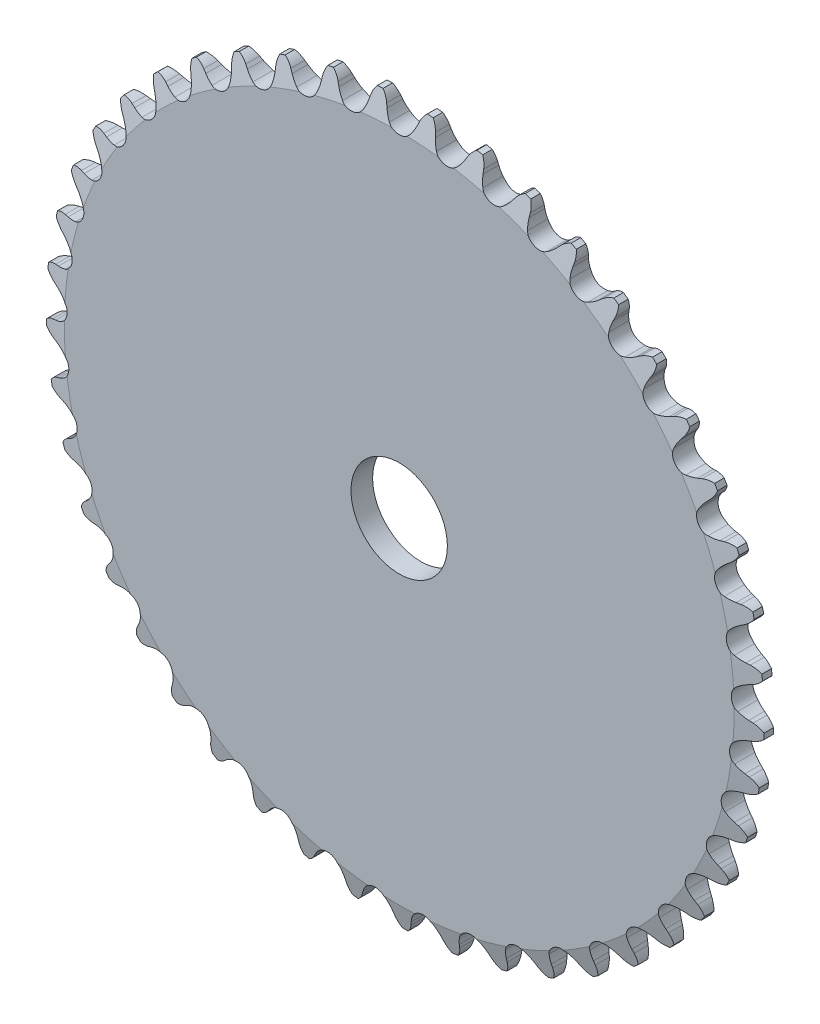
SolidWorks part; units mm, degrees
ref_plane "Front Plane" through (0, 0, 0) normal (0, 0, 1) x (1, 0, 0)
ref_plane "Top Plane" through (0, 0, 0) normal (0, 1, 0) x (1, 0, 0)
ref_plane "Right Plane" through (0, 0, 0) normal (1, 0, 0) x (0, 0, -1)
sketch "Sketch0" plane through (0, 0, 0) normal (0, 0, 1) x (1, 0, 0)
  line L0 (4.7625, -68.1069) -> (0, 0) construction
  line L1 (0, 0) -> (14.1948, -66.7813) construction
  line L2 (0, 0) -> (-4.7625, -68.1069) construction
  line L3 (4.7625, -68.1069) -> (14.1948, -66.7813) construction
  line L4 (4.7625, -68.1069) -> (-4.7625, -68.1069) construction
  line L5 (8.0591, -68.7521) -> (7.7638, -68.0754)
  line L6 (4.7625, -68.1069) -> (0, -68.4399) construction
  line L7 (1.5878, -69.2046) -> (1.786, -68.4934)
  line L8 (0, -68.1069) -> (0, -70.9644) construction
  line L9 (6.7374, -66.4301) -> (1.6645, -70.7373) construction
  line L10 (0, 0) -> (0, -68.1069) construction
  line L11 (7.7638, -68.0754) -> (1.6645, -70.7373) construction
  line L12 (0, -70.9644) -> (0, -71.4516) construction
  line L13 (11.8053, -67.1171) -> (8.0591, -68.7521) construction
  circle A0 centre (0, 0) radius 70.9644 construction
  circle A1 centre (0, 0) radius 68.2732 construction
  arc A2 (-2.4904, -72.1919) -> (12.5134, -71.1427) centre (0, 0) ccw
  circle A3 centre (0, 0) radius 71.4516 construction
  circle A4 centre (4.7625, -68.1069) radius 2.54 construction
  arc A7 (6.7374, -66.4301) -> (2.5734, -66.7212) centre (4.7625, -68.1069) ccw
  circle A8 centre (4.7625, -68.1069) radius 2.5908 construction
  arc A9 (8.0591, -68.7521) -> (12.5134, -71.1427) centre (11.8053, -67.1171) ccw
  arc A10 (7.7638, -68.0754) -> (6.7374, -66.4301) centre (1.6645, -70.7373) ccw
  arc A11 (1.5878, -69.2046) -> (-2.4904, -72.1919) centre (-2.3495, -68.1069) cw
  arc A12 (1.786, -68.4934) -> (2.5734, -66.7212) centre (8.1964, -70.2805) cw
  dimension "D1" = 2.5908
  dimension "R" = 2.5908
sketch "Sketch1" plane through (0, 0, 0) normal (1, 0, 0) x (0, 0, -1)
  line L0 (2.1336, 0) -> (-2.1336, 0)
  line L1 (-2.1336, 0) -> (-2.1336, 66.2019)
  line L2 (-2.1336, 66.2019) -> (-0.943, 70.9644)
  line L3 (-0.943, 70.9644) -> (0.943, 70.9644)
  line L4 (0.943, 70.9644) -> (2.1336, 66.2019)
  line L5 (2.1336, 66.2019) -> (2.1336, 0)
  line L7 (0, 70.9644) -> (0, 0) construction
  line L8 (-2.1336, 66.2019) -> (2.1336, 66.2019) construction
  line L9 (0, 70.9644) -> (0, -70.9644) construction
  line L10 (-2.1336, 66.2019) -> (-2.1336, 70.9644) construction
  line L11 (-2.1336, 70.9644) -> (-0.943, 70.9644) construction
  line L12 (0.943, 70.9644) -> (2.1336, 70.9644) construction
  line L13 (2.1336, 70.9644) -> (2.1336, 66.2019) construction
revolve "Revolve1" add sketch "Sketch1" angle 360 mid plane about L0
extrude "Cut-Extrude1" cut sketch "Sketch0" against normal through all and the other way through all
pattern_circular "CirPattern1" count 45 over 360 about axis through (0, 0, 0) along (0, 0, 1) of "Cut-Extrude1"
sketch "Sketch2" plane through (0, 0, 0) normal (0, 0, 1) x (1, 0, 0)
  circle A0 centre (0, 0) radius 7.5406 construction
  circle A1 centre (0, 0) radius 30.1625
  circle A2 centre (0, 0) radius 70.993 construction
  dimension "Bore" = 15.0812
  dimension "Hub Dia." = 60.325
  dimension "OD" = 141.986
sketch "Sketch3" plane through (0, 0, 0) normal (0, 0, 1) x (1, 0, 0)
  circle A0 centre (0, 0) radius 7.5406 construction
  circle A1 centre (0, 0) radius 7.5406
  circle A2 centre (0, 0) radius 70.993 construction
  circle A3 centre (0, 0) radius 70.993
extrude "Cut-Extrude2" cut sketch "Sketch3" along normal through all and the other way through all flip side to cut
sketch "Sketch5" plane through (0, 0, 2.1336) normal (0, 0, 1) x (1, 0, 0)
  circle A0 centre (0, 0) radius 9.525
  dimension "D1" = 19.05
extrude "Cut-Extrude3" cut sketch "Sketch5" against normal up to next
equation "\"360/N@Sketch0\" = 360/\"Teeth@CirPattern1\""
equation "\"Ds@Sketch0\" = 1.005 * \"Dr@Sketch0\" + 0.003"
equation "\"R@Sketch0\" = 1/2 * \"Ds@Sketch0\""
equation "\"A@Sketch0\" = 35 +  ( 60 / \"Teeth@CirPattern1\" ) "
equation "\"B@Sketch0\" = 18 -  ( 56 / \"Teeth@CirPattern1\" )"
equation "\"ac@Sketch0\" = 0.8 * \"Dr@Sketch0\""
equation "\"ab@Sketch0\" = 1.4 * \"Dr@Sketch0\""
equation "\"J@Sketch0\" = 0.3 * \"Pitch@Sketch0\""
equation "\"h@Sketch1\" = \"Pitch@Sketch0\" / 2"
equation "\"g@Sketch1\" = \"h@Sketch1\" / 4"
